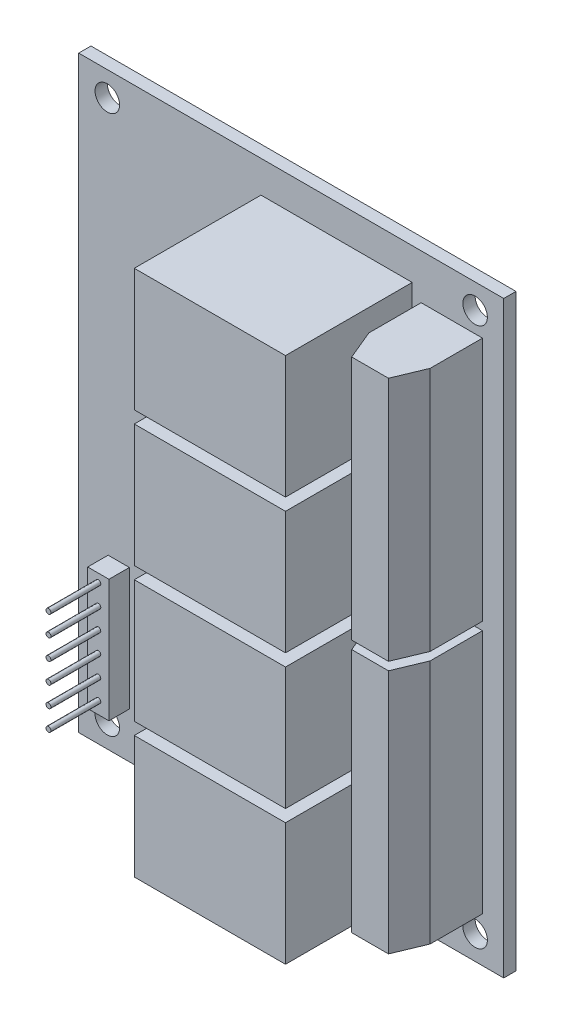
SolidWorks part; units mm, degrees
ref_plane "Alzado" through (0, 0, 0) normal (0, 0, 1) x (1, 0, 0)
ref_plane "Planta" through (0, 0, 0) normal (0, 1, 0) x (1, 0, 0)
ref_plane "Vista lateral" through (0, 0, 0) normal (1, 0, 0) x (0, 0, -1)
sketch "Croquis1" plane through (0, 0, 0) normal (0, 0, 1) x (1, 0, 0)
  line L1 (-26, -36) -> (26, -36)
  line L2 (-26, -36) -> (-26, 36)
  line L3 (-26, 36) -> (26, 36)
  line L4 (26, -36) -> (26, 36)
  line L5 (-26, -36) -> (26, 36) construction
  line L6 (-26, 36) -> (26, -36) construction
  point P0 (0, 0)
  dimension "D1" = 72
  dimension "D2" = 52
extrude "Saliente-Extruir1" add sketch "Croquis1" along normal mid plane 1.5
sketch "Croquis2" plane through (0, 0, 0.75) normal (0, 0, 1) x (1, 0, 0)
  line L0 (0, 0) -> (0, 47.9624) construction
  line L1 (38.7874, 0) -> (-51.6077, 0) construction
  circle A0 centre (-22.5, 33) radius 1.5
  circle A1 centre (22.5, 33) radius 1.5
  circle A2 centre (-22.5, -33) radius 1.5
  circle A3 centre (22.5, -33) radius 1.5
  dimension "D3" = 3
  dimension "D1" = 22.5
  dimension "D2" = 33
extrude "Cortar-Extruir1" cut sketch "Croquis2" against normal blind 1.5
sketch "Croquis3" plane through (0, 0, 0.75) normal (0, 0, 1) x (1, 0, 0)
  line L0 (-26, -36) -> (26, -36) construction
  line L1 (14.8, -17.4) -> (-3.7, -17.4)
  line L2 (14.8, -17.4) -> (14.8, -32.4)
  line L3 (14.8, -32.4) -> (-3.7, -32.4)
  line L4 (-3.7, -17.4) -> (-3.7, -32.4)
  line L5 (14.8, -17.4) -> (-3.7, -32.4) construction
  line L6 (14.8, -32.4) -> (-3.7, -17.4) construction
  line L7 (26, -36) -> (26, 36) construction
  line L8 (14.8, -0.9) -> (14.8, -15.9)
  line L9 (14.8, -0.9) -> (-3.7, -0.9)
  line L10 (-3.7, -0.9) -> (-3.7, -15.9)
  line L11 (14.8, -15.9) -> (-3.7, -15.9)
  line L12 (14.8, 15.6) -> (14.8, 0.6)
  line L13 (14.8, 15.6) -> (-3.7, 15.6)
  line L14 (-3.7, 15.6) -> (-3.7, 0.6)
  line L15 (14.8, 0.6) -> (-3.7, 0.6)
  line L16 (14.8, 32.1) -> (14.8, 17.1)
  line L17 (14.8, 32.1) -> (-3.7, 32.1)
  line L18 (-3.7, 32.1) -> (-3.7, 17.1)
  line L19 (14.8, 17.1) -> (-3.7, 17.1)
  point P0 (5.55, -24.9)
  dimension "D1" = 18.5
  dimension "D2" = 15
  dimension "D3" = 3.6
  dimension "D4" = 11.2
  dimension "D6" = 1.5
  dimension "D5" = 4
extrude "Saliente-Extruir2" add sketch "Croquis3" along normal blind 15.5
sketch "Croquis4" plane through (0, 0, 0.75) normal (0, 0, 1) x (1, 0, 0)
  line L0 (26, -36) -> (26, 36) construction
  line L1 (15.9, -0.5) -> (23.4, -0.5)
  line L2 (15.9, -0.5) -> (15.9, -30.5)
  line L3 (15.9, -30.5) -> (23.4, -30.5)
  line L4 (23.4, -0.5) -> (23.4, -30.5)
  line L5 (-26, -36) -> (26, -36) construction
  line L6 (-35.466, 0) -> (67.4625, 0) construction
  line L7 (15.9, 30.5) -> (23.4, 30.5)
  line L8 (23.4, 0.5) -> (23.4, 30.5)
  line L9 (15.9, 0.5) -> (23.4, 0.5)
  line L10 (15.9, 0.5) -> (15.9, 30.5)
  dimension "D1" = 30
  dimension "D2" = 7.5
  dimension "D3" = 2.6
  dimension "D4" = 5.5
extrude "Saliente-Extruir3" add sketch "Croquis4" along normal blind 10
sketch "Croquis5" plane through (0, -30.5, 0) normal (0, -1, 0) x (1, 0, 0)
  line L0 (15.9, 7.15) -> (17.4, 10.75)
  line L1 (19.65, 10.75) -> (19.65, 0.75) construction
  line L2 (23.4, 7.15) -> (21.9, 10.75)
  line L4 (15.9, 0.75) -> (23.4, 0.75)
  line L5 (23.4, 0.75) -> (23.4, 10.75)
  line L6 (23.4, 10.75) -> (15.9, 10.75)
  line L7 (15.9, 10.75) -> (15.9, 0.75)
  line L8 (15.9, 0.75) -> (23.4, 0.75)
  line L9 (23.4, 0.75) -> (23.4, 10.75)
  line L10 (23.4, 10.75) -> (15.9, 10.75)
  line L11 (15.9, 10.75) -> (15.9, 0.75)
  line M8 (23.4, 0.75) -> (23.4, 10.75)
  line M9 (23.4, 10.75) -> (15.9, 10.75)
  line M10 (15.9, 10.75) -> (15.9, 0.75)
  dimension "D2" = 2.25
  dimension "D3" = 6.4
  dimension "D1" = 0
extrude "Cortar-Extruir2" cut sketch "Croquis5" against normal blind 80 contours L0 M10 M9 | L2 M8 M9
sketch "Croquis6" plane through (0, 0, 0.75) normal (0, 0, 1) x (1, 0, 0)
  line L0 (-26, -36) -> (26, -36) construction
  line L1 (-19.8, -30.4) -> (-22.4, -30.4)
  line L2 (-19.8, -30.4) -> (-19.8, -15.4)
  line L3 (-19.8, -15.4) -> (-22.4, -15.4)
  line L4 (-22.4, -30.4) -> (-22.4, -15.4)
  line L5 (-26, 36) -> (-26, -36) construction
  dimension "D1" = 5.6
  dimension "D2" = 2.6
  dimension "D3" = 3.6
  dimension "D4" = 15
extrude "Saliente-Extruir4" add sketch "Croquis6" along normal blind 2.5
sketch "Croquis7" plane through (0, 0, 3.25) normal (0, 0, 1) x (1, 0, 0)
  line L0 (-21.1, -15.4) -> (-21.1, -30.4) construction
  line L1 (-19.8, -15.4) -> (-22.4, -15.4) construction
  line L2 (-22.4, -30.4) -> (-19.8, -30.4) construction
  circle A0 centre (-21.1, -28.9) radius 0.3
  circle A1 centre (-21.1, -26.4) radius 0.3
  circle A2 centre (-21.1, -23.9) radius 0.3
  circle A3 centre (-21.1, -21.4) radius 0.3
  circle A4 centre (-21.1, -18.9) radius 0.3
  circle A5 centre (-21.1, -16.4) radius 0.3
  dimension "D1" = 0.6
  dimension "D2" = 1.5
  dimension "D4" = 2.5
  dimension "D3" = 6
extrude "Saliente-Extruir5" add sketch "Croquis7" along normal blind 6.1
